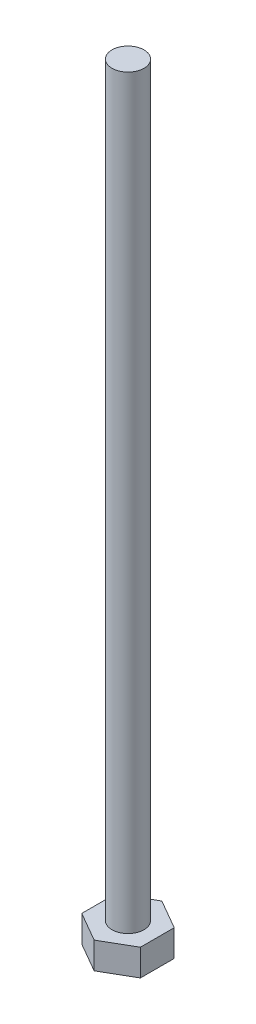
SolidWorks part; units mm, degrees
ref_plane "Front Plane" through (0, 0, 0) normal (0, 0, 1) x (1, 0, 0)
ref_plane "Top Plane" through (0, 0, 0) normal (0, 1, 0) x (1, 0, 0)
ref_plane "Right Plane" through (0, 0, 0) normal (1, 0, 0) x (0, 0, -1)
sketch "Sketch1" plane through (0, 0, 0) normal (0, 1, 0) x (1, 0, 0)
  line L1 (2.75, 1.5877) -> (0, 3.1754)
  line L2 (0, 3.1754) -> (-2.75, 1.5877)
  line L3 (-2.75, 1.5877) -> (-2.75, -1.5877)
  line L4 (-2.75, -1.5877) -> (0, -3.1754)
  line L5 (0, -3.1754) -> (2.75, -1.5877)
  line L6 (2.75, -1.5877) -> (2.75, 1.5877)
  circle A0 centre (0, 0) radius 2.75 construction
  dimension "D1" = 5.5
extrude "Boss-Extrude1" add sketch "Sketch1" along normal blind 2.5
sketch "Sketch2" plane through (0, 2.5, 0) normal (0, 1, 0) x (1, 0, 0)
  circle A0 centre (0, 0) radius 1.5
  dimension "D1" = 3
extrude "Boss-Extrude2" add sketch "Sketch2" along normal blind 70
